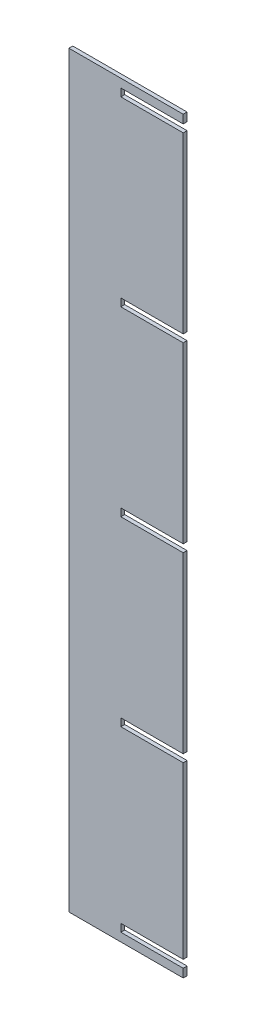
SolidWorks part; units mm, degrees
material "Oak"
ref_plane "Front Plane" through (0, 0, 0) normal (0, 0, 1) x (1, 0, 0)
ref_plane "Top Plane" through (0, 0, 0) normal (0, 1, 0) x (1, 0, 0)
ref_plane "Right Plane" through (0, 0, 0) normal (1, 0, 0) x (0, 0, -1)
sketch "Sketch1" plane through (0, 0, 0) normal (0, 0, 1) x (1, 0, 0)
  line L0 (26087.862, 6999.9516) -> (26367.262, 6999.9516)
  line L1 (26367.262, 6999.9516) -> (26367.262, 8828.7516)
  line L2 (26367.262, 8828.7516) -> (26087.862, 8828.7516)
  line L3 (26087.862, 8828.7516) -> (26087.862, 6999.9516)
  line L4 (26214.862, 7020.6526) -> (26367.262, 7020.6526)
  line L5 (26367.262, 7020.6526) -> (26367.262, 7039.4486)
  line L6 (26367.262, 7039.4486) -> (26214.862, 7039.4486)
  line L7 (26214.862, 7039.4486) -> (26214.862, 7020.6526)
  line L8 (26214.862, 8789.2546) -> (26367.262, 8789.2546)
  line L9 (26367.262, 8789.2546) -> (26367.262, 8808.0506)
  line L10 (26367.262, 8808.0506) -> (26214.862, 8808.0506)
  line L11 (26214.862, 8808.0506) -> (26214.862, 8789.2546)
  line L12 (26214.862, 8344.7546) -> (26367.262, 8344.7546)
  line L13 (26367.262, 8344.7546) -> (26367.262, 8363.5506)
  line L14 (26367.262, 8363.5506) -> (26214.862, 8363.5506)
  line L15 (26214.862, 8363.5506) -> (26214.862, 8344.7546)
  line L16 (26214.862, 7900.2546) -> (26367.262, 7900.2546)
  line L17 (26367.262, 7900.2546) -> (26367.262, 7919.0506)
  line L18 (26367.262, 7919.0506) -> (26214.862, 7919.0506)
  line L19 (26214.862, 7919.0506) -> (26214.862, 7900.2546)
  line L20 (26214.862, 7455.7546) -> (26367.262, 7455.7546)
  line L21 (26367.262, 7455.7546) -> (26367.262, 7474.5506)
  line L22 (26367.262, 7474.5506) -> (26214.862, 7474.5506)
  line L23 (26214.862, 7474.5506) -> (26214.862, 7455.7546)
extrude "Boss-Extrude1" add sketch "Sketch1" along normal blind 9.398 contours L23 L22 L1 L16 L19 L18 L12 L15 L14 L8 L11 L10 L2 L3 L0 L4 L7 L6 L20
